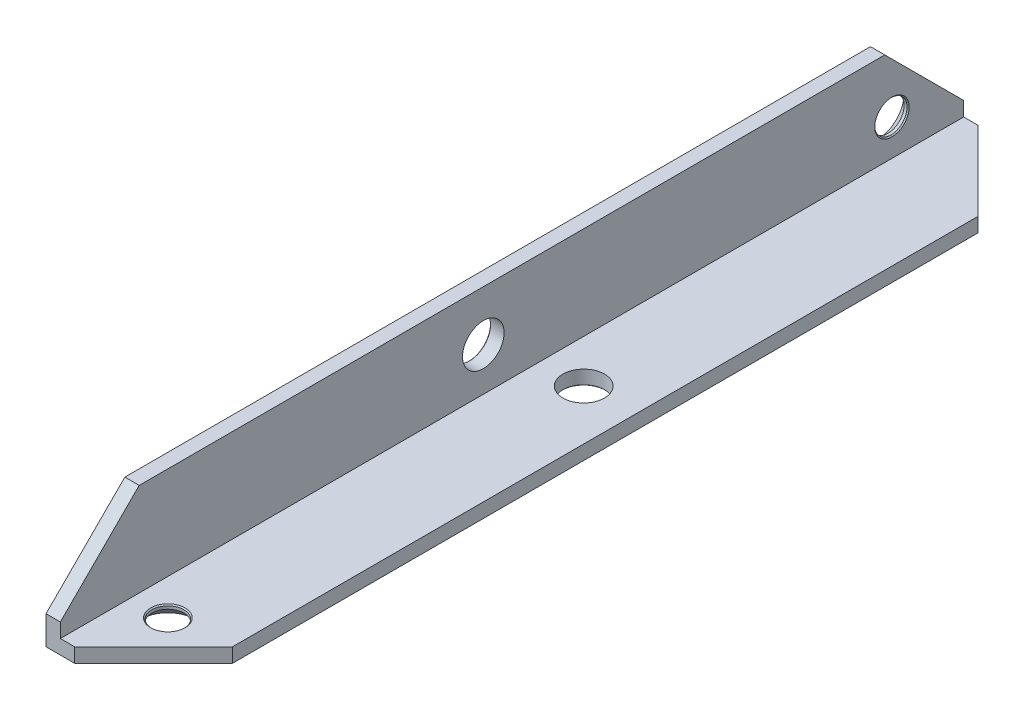
SolidWorks part; units mm, degrees
ref_plane "Спереди" through (0, 0, 0) normal (0, 0, 1) x (1, 0, 0)
ref_plane "Сверху" through (0, 0, 0) normal (0, 1, 0) x (1, 0, 0)
ref_plane "Справа" through (0, 0, 0) normal (1, 0, 0) x (0, 0, -1)
sketch "Эскиз1" plane through (0, 0, 0) normal (0, 0, 1) x (1, 0, 0)
  line L0 (0, 0) -> (0, 15)
  line L1 (0, 15) -> (2, 15)
  line L2 (2, 15) -> (2, 2)
  line L3 (2, 2) -> (15, 2)
  line L4 (15, 2) -> (15, 0)
  line L5 (15, 0) -> (0, 0)
  dimension "D1" = 2
  dimension "D2" = 15
extrude "Бобышка-Вытянуть1" add sketch "Эскиз1" along normal blind 126
chamfer "Фаска1" distance 11 angle 45 4 edges at (1, 15, 0) (15, 1, 0) (15, 1, 126) (1, 15, 126)
hole_wizard "Зенковка для винта с потайной головкой M41" positions "Эскиз3" profile "Эскиз2" countersink size "M4" standard "DIN" end condition through all
sketch "Эскиз3" plane through (0, 0, 0) normal (0, -1, 0) x (1, 0, 0)
  line L0 (0, 126) -> (0, 0) construction
  line L1 (0, 126) -> (4, 126) construction
  point P0 (7, 116)
  dimension "D1" = 7
  dimension "D2" = 10
sketch "Эскиз2" plane through (7, 0, 116) normal (1, 0, 0) x (0, 0, -1)
  line L0 (0, 0) -> (0, 2)
  line L1 (0, 2) -> (2.4, 2)
  line L2 (2.25, 1.85) -> (2.25, 1.45)
  line L3 (2.25, 1.45) -> (3.7, 0)
  line L5 (3.7, 0) -> (0, 0)
  line L6 (-2.25, 1.45) -> (-3.7, 0) construction
  line L7 (2.4, 2) -> (2.25, 1.85)
  line L8 (-2.4, 2) -> (-2.25, 1.85) construction
  line L11 (0, -6.35) -> (0, 107.95) construction
  dimension "Диаметр сквозного отверстия" = 4.5
  dimension "Глубина сквозного отверстия" = 2
  dimension "Диаметр передней зенковки" = 7.4
  dimension "Угол передней зенковки" = 90
  dimension "Диаметр задней зенковки" = 4.8
  dimension "Угол задней зенковки" = 90
hole_wizard "Зенковка для винта с потайной головкой M42" positions "Эскиз5" profile "Эскиз4" countersink size "M4" standard "DIN" end condition through all
sketch "Эскиз5" plane through (0, 0, 0) normal (-1, 0, 0) x (0, 0, 1)
  line L0 (126, 0) -> (0, 0) construction
  line L1 (0, 4) -> (0, 0) construction
  point P0 (10, 7)
  dimension "D1" = 7
  dimension "D2" = 10
sketch "Эскиз4" plane through (0, 7, 10) normal (0, 1, 0) x (0, 0, 1)
  line L0 (0, 0) -> (0, 2)
  line L1 (0, 2) -> (2.4, 2)
  line L2 (2.25, 1.85) -> (2.25, 1.45)
  line L3 (2.25, 1.45) -> (3.7, 0)
  line L5 (3.7, 0) -> (0, 0)
  line L6 (-2.25, 1.45) -> (-3.7, 0) construction
  line L7 (2.4, 2) -> (2.25, 1.85)
  line L8 (-2.4, 2) -> (-2.25, 1.85) construction
  line L11 (0, -6.35) -> (0, 107.95) construction
  dimension "Диаметр сквозного отверстия" = 4.5
  dimension "Глубина сквозного отверстия" = 2
  dimension "Диаметр передней зенковки" = 7.4
  dimension "Угол передней зенковки" = 90
  dimension "Диаметр задней зенковки" = 4.8
  dimension "Угол задней зенковки" = 90
hole_wizard "Отверстие с зазором M51" positions "Эскиз7" profile "Эскиз6" hole size "M5" standard "Ansi (метрические)"
sketch "Эскиз7" plane through (0, 0, 0) normal (0, -1, 0) x (1, 0, 0)
  line L0 (0, 126) -> (0, 0) construction
  circle A0 centre (7, 116) radius 2.25 construction
  point P0 (8, 59)
  dimension "D1" = 57
  dimension "D2" = 8
sketch "Эскиз6" plane through (8, 0, 59) normal (1, 0, 0) x (0, 0, -1)
  line L0 (0, 0) -> (0, 4.7425)
  line L1 (0, 4.7425) -> (2.9, 3)
  line L2 (2.9, 3) -> (2.9, 0.1)
  line L3 (2.9, 0.1) -> (3, 0)
  line L5 (3, 0) -> (0, 0)
  line L6 (-2.9, 0.1) -> (-3, 0) construction
  line L10 (0, 4.7425) -> (-2.9, 3) construction
  line L11 (0, -6.35) -> (0, 107.95) construction
  dimension "Диаметр отверстия" = 5.8
  dimension "Глубина отверстия" = 3
  dimension "Диаметр передней зенковки" = 6
  dimension "Угол передней зенковки" = 90
  dimension "Угол заточки сверла" = 118
hole_wizard "Отверстие с зазором M52" positions "Эскиз9" profile "Эскиз8" hole size "M5" standard "Ansi (метрические)"
sketch "Эскиз9" plane through (0, 0, 0) normal (-1, 0, 0) x (0, 0, 1)
  line L0 (126, 0) -> (0, 0) construction
  circle A0 centre (10, 7) radius 2.25 construction
  point P0 (67, 8)
  dimension "D1" = 57
  dimension "D2" = 8
sketch "Эскиз8" plane through (0, 8, 67) normal (0, 1, 0) x (0, 0, 1)
  line L0 (0, 0) -> (0, 4.7425)
  line L1 (0, 4.7425) -> (2.9, 3)
  line L2 (2.9, 3) -> (2.9, 0.1)
  line L3 (2.9, 0.1) -> (3, 0)
  line L5 (3, 0) -> (0, 0)
  line L6 (-2.9, 0.1) -> (-3, 0) construction
  line L10 (0, 4.7425) -> (-2.9, 3) construction
  line L11 (0, -6.35) -> (0, 107.95) construction
  dimension "Диаметр отверстия" = 5.8
  dimension "Глубина отверстия" = 3
  dimension "Диаметр передней зенковки" = 6
  dimension "Угол передней зенковки" = 90
  dimension "Угол заточки сверла" = 118
